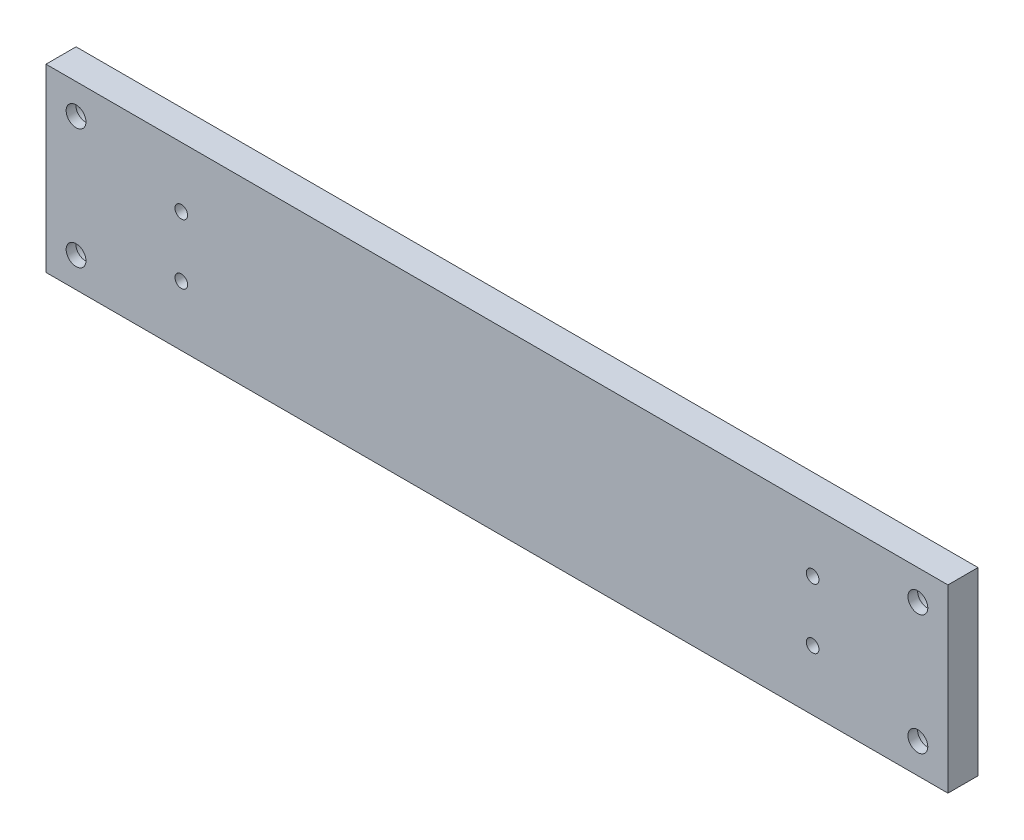
SolidWorks part; units mm, degrees
material "A3钢"
ref_plane "前视基准面" through (0, 0, 0) normal (0, 0, 1) x (1, 0, 0)
ref_plane "上视基准面" through (0, 0, 0) normal (0, 1, 0) x (1, 0, 0)
ref_plane "右视基准面" through (0, 0, 0) normal (1, 0, 0) x (0, 0, -1)
sketch "草图1" plane through (0, 0, 0) normal (0, 0, 1) x (1, 0, 0)
  line L0 (0, 0) -> (300, 0)
  line L1 (300, 0) -> (300, -60)
  line L4 (0, -60) -> (0, 0)
  line L5 (0, -60) -> (300, -60)
  dimension "D1" = 300
  dimension "D2" = 60
extrude "凸台-拉伸1" add sketch "草图1" along normal mid plane 10
sketch "草图4" plane through (0, 0, 5) normal (0, 0, 1) x (1, 0, 0)
  line L0 (7.5, 0) -> (7.5, -10) construction
  line L1 (300, 0) -> (0, 0) construction
  line L2 (0, 0) -> (0, -60) construction
  dimension "D1" = 10
  dimension "D2" = 7.5
ref_plane "基准面1" through (150, 0, 0) normal (-1, 0, 0) x (0, 0, 1)
sketch "草图6" plane through (0, -60, 0) normal (0, -1, 0) x (1, 0, 0)
  line L0 (150, 5) -> (150, -43.0437) construction
  line L1 (0, 5) -> (300, 5) construction
  line L2 (30, 0) -> (270, 0) construction
  line L3 (0, -5) -> (300, -5) construction
  dimension "D1" = 240
hole_wizard "M6 螺纹孔1" positions "3D草图2" profile "草图7" tap size "M6" standard "GB"
sketch3d "3D草图2"
  line L1 (30, -60, 0) -> (270, -60, 0) construction
  point P0 (30, -60, 0)
  point P3 (270, -60, 0)
  point P10 (150, -60, 0)
sketch "草图7" plane through (30, -60, 0) normal (1, 0, 0) x (0, 0, -1)
  line L0 (0, 0) -> (0, 16.5022)
  line L1 (0, 16.5022) -> (2.5, 15)
  line L2 (2.5, 15) -> (2.5, 0)
  line L5 (2.5, 0) -> (0, 0)
  line L10 (0, 16.5022) -> (-2.5, 15) construction
  line L11 (0, -6.35) -> (0, 107.95) construction
  dimension "螺纹孔钻头直径" = 5
  dimension "螺纹孔钻头深度" = 15
  dimension "导头角度" = 118
cosmetic thread "孔螺蚊线1" parameters "D1"=12, "D2"=6
cosmetic thread "孔螺蚊线2" parameters "D1"=12, "D2"=6
cosmetic thread "孔螺蚊线3" parameters "D1"=12, "D2"=6
sketch "草图8" plane through (0, 0, -5) normal (0, 0, -1) x (-1, 0, 0)
  line L0 (-150, 0) -> (-150, -101.9413) construction
  line L1 (-300, 0) -> (0, 0) construction
  line L2 (-300, -30) -> (51.4215, -30) construction
  line L3 (-300, -60) -> (-300, 0) construction
  line L5 (-290, -50) -> (-10, -50)
  line L6 (-290, -50) -> (-290, -10)
  line L7 (-290, -10) -> (-10, -10)
  line L8 (-10, -50) -> (-10, -10)
  line L9 (-290, -50) -> (-10, -10) construction
  line L10 (-290, -10) -> (-10, -50) construction
  point P8 (-150, -30)
  dimension "D1" = 40
  dimension "D2" = 280
hole_wizard "打孔尺寸(%根据)内六角圆柱头螺钉的类型1" positions "3D草图4" profile "草图10" counterbore size "M6" standard "GB" end condition through all
sketch3d "3D草图4"
  point P0 (10, -10, -5)
  point P3 (10, -50, -5)
  point P6 (290, -10, -5)
  point P9 (290, -50, -5)
sketch "草图10" plane through (10, -10, -5) normal (1, 0, 0) x (0, 1, 0)
  line L0 (0, 0) -> (0, 10)
  line L1 (0, 10) -> (3.3, 10)
  line L3 (3.3, 10) -> (3.3, 6.8)
  line L4 (3.3, 6.8) -> (5.5, 6.8)
  line L5 (5.5, 6.8) -> (5.5, 0)
  line L7 (5.5, 0) -> (0, 0)
  line L11 (0, -6.35) -> (0, 107.95) construction
  dimension "通孔孔直径" = 6.6
  dimension "通孔孔深度" = 10
  dimension "柱形沉头孔直径" = 11
  dimension "柱形沉头孔深度" = 6.8
sketch "草图11" plane through (0, 0, -5) normal (0, 0, -1) x (-1, 0, 0)
  line L0 (-300, -30) -> (0, -30) construction
  line L1 (-300, -60) -> (-300, 0) construction
  line L2 (0, 0) -> (0, -60) construction
  line L3 (-45, -20) -> (-45, -40) construction
  dimension "D1" = 45
  dimension "D2" = 20
sketch "草图13" plane through (0, 0, -5) normal (0, 0, -1) x (-1, 0, 0)
  line L0 (-220, -20) -> (-220, -40) construction
  line L1 (-300, 0) -> (0, 0) construction
  line L2 (-300, -60) -> (-300, 0) construction
  dimension "D1" = 20
  dimension "D2" = 20
  dimension "D3" = 80
hole_wizard "M5 螺纹孔1" positions "3D草图5" profile "草图14" tap size "M5" standard "GB" end condition through all
sketch3d "3D草图5"
  point P0 (45, -20, -5)
  point P3 (45, -40, -5)
sketch "草图14" plane through (45, -20, -5) normal (1, 0, 0) x (0, 1, 0)
  line L0 (0, 0) -> (0, 10)
  line L1 (0, 10) -> (2.1, 10)
  line L2 (2.1, 10) -> (2.1, 0)
  line L5 (2.1, 0) -> (0, 0)
  line L11 (0, -6.35) -> (0, 107.95) construction
  dimension "通孔螺纹孔钻头直径" = 4.2
  dimension "通孔螺纹孔钻头深度" = 10
cosmetic thread "孔螺蚊线4" parameters "D2"=5
cosmetic thread "孔螺蚊线5" parameters "D2"=5
ref_plane "基准面2" through (150, 0, 0) normal (1, 0, 0) x (0, 0, -1)
mirror "镜向1" about plane through (150, 0, 0) normal (1, 0, 0) of "M5 螺纹孔1"
